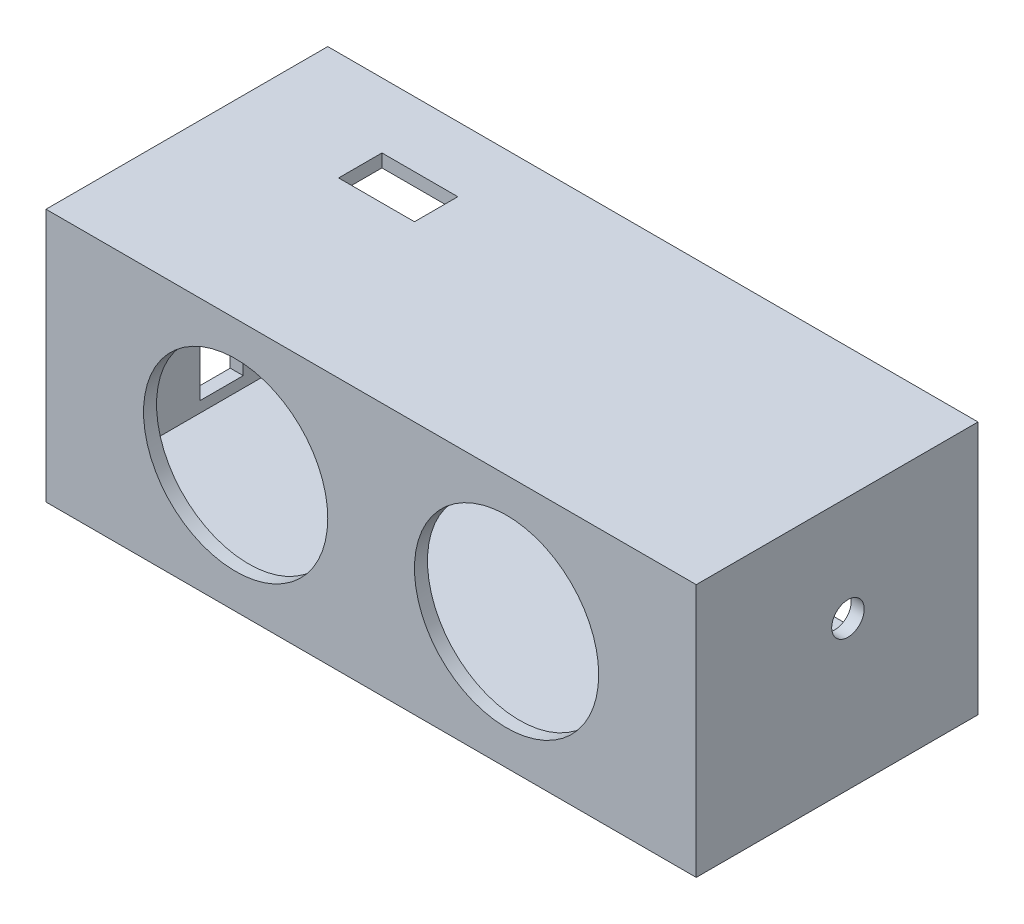
SolidWorks part; units mm, degrees
ref_plane "Front Plane" through (0, 0, 0) normal (0, 0, 1) x (1, 0, 0)
ref_plane "Top Plane" through (0, 0, 0) normal (0, 1, 0) x (1, 0, 0)
ref_plane "Right Plane" through (0, 0, 0) normal (1, 0, 0) x (0, 0, -1)
sketch3d "3DSketch1"
  line L0 (-25.7407, -9.0712, 0) -> (34.2593, -9.0712, 0)
  line L1 (-25.7407, 14.3288, 0) -> (34.2593, 14.3288, 0)
  line L2 (-25.7407, 14.3288, 0) -> (-25.7407, -9.0712, 0)
  line L4 (34.2593, 14.3288, 0) -> (34.2593, -9.0712, 0)
  circle A0 centre (-8.2407, 2.6288, 0) radius 8.5
  circle A1 centre (16.7593, 2.6288, 0) radius 8.5
  point P10 (-8.2407, 2.6288, 8.5)
  point P13 (16.7593, 2.6288, 8.5)
  dimension "D5" = 17
  dimension "D6" = 17
  dimension "D2" = 17.5
  dimension "D1" = 23.4
  dimension "D3" = 17.5
  dimension "D4" = 25
extrude "Boss-Extrude3" add sketch "3DSketch1" along direction (0, 0, 1) on the side of the normal blind 1.2
sketch "Sketch3" plane through (0, 0, 0) normal (0, 0, 1) x (1, 0, 0)
  line L1 (-25.7407, 14.3288) -> (34.2593, 14.3288)
  line L2 (-25.7407, 14.3288) -> (-25.7407, -9.0712)
  line L3 (-25.7407, -9.0712) -> (34.2593, -9.0712)
  line L4 (34.2593, 14.3288) -> (34.2593, -9.0712)
  line L5 (-24.5407, 13.1288) -> (33.0593, 13.1288)
  line L6 (-24.5407, 13.1288) -> (-24.5407, -7.8712)
  line L7 (-24.5407, -7.8712) -> (33.0593, -7.8712)
  line L8 (33.0593, 13.1288) -> (33.0593, -7.8712)
  dimension "D1" = 1.2
  dimension "D2" = 1.2
  dimension "D3" = 1.2
  dimension "D4" = 1.2
extrude "Boss-Extrude4" add sketch "Sketch3" against normal blind 26
sketch "Sketch6" plane through (0, -9.0712, 0) normal (0, -1, 0) x (1, 0, 0)
  line L0 (-25.7407, -26) -> (34.2593, -26) construction
  line L1 (34.2593, 0) -> (33.0593, 0)
  line L2 (34.2593, 0) -> (34.2593, -1.2)
  line L3 (34.2593, -1.2) -> (33.0593, -1.2)
  line L4 (33.0593, 0) -> (33.0593, -1.2)
  line L5 (33.0593, -1.2) -> (20.5593, -1.2)
  line L6 (33.0593, -1.2) -> (33.0593, -19.2)
  line L7 (33.0593, -19.2) -> (20.5593, -19.2)
  line L8 (20.5593, -1.2) -> (20.5593, -19.2)
  line L9 (20.5593, -9.2) -> (23.5593, -9.2)
  line L10 (20.5593, -9.2) -> (20.5593, -17.2)
  line L11 (20.5593, -17.2) -> (23.5593, -17.2)
  line L12 (23.5593, -9.2) -> (23.5593, -17.2)
  dimension "D1" = 1.2
  dimension "D2" = 1.2
  dimension "D3" = 18
  dimension "D4" = 12.5
  dimension "D5" = 8
  dimension "D6" = 2
  dimension "D7" = 3
extrude "Cut-Extrude1" cut sketch "Sketch6" against normal blind 4 contours L12 L9 L8 L11
sketch "Sketch7" plane through (0, 14.3288, 0) normal (0, 1, 0) x (1, 0, 0)
  line L0 (-25.7407, 0) -> (-25.7407, 26) construction
  line L1 (-25.7407, 26) -> (-7.7407, 26)
  line L2 (-25.7407, 26) -> (-25.7407, 20)
  line L3 (-25.7407, 20) -> (-7.7407, 20)
  line L4 (-7.7407, 26) -> (-7.7407, 20)
  line L5 (-7.7407, 20) -> (-14.7407, 20)
  line L6 (-7.7407, 20) -> (-7.7407, 16)
  line L7 (-7.7407, 16) -> (-14.7407, 16)
  line L8 (-14.7407, 20) -> (-14.7407, 16)
  dimension "D1" = 6
  dimension "D2" = 4
  dimension "D3" = 7
  dimension "D4" = 11
extrude "Cut-Extrude2" cut sketch "Sketch7" against normal blind 4 contours L3 L8 L7 L6
sketch "Sketch9" plane through (34.2593, 0, 0) normal (1, 0, 0) x (0, 0, -1)
  line L0 (0, 4.6288) -> (26, 4.6288)
  line L1 (26, -9.0712) -> (0, -9.0712)
  line L2 (26, -9.0712) -> (26, 14.3288)
  line L3 (26, 14.3288) -> (0, 14.3288)
  line L4 (0, -9.0712) -> (0, 14.3288)
  line L5 (26, 4.6288) -> (20, 4.6288)
  line L6 (20, 4.6288) -> (14, 4.6288)
  circle A0 centre (14, 4.6288) radius 6
  circle A1 centre (14, 4.6288) radius 1.5
  dimension "D4" = 3
  dimension "D1" = 13.7
  dimension "D2" = 6
  dimension "D3" = 6
extrude "Cut-Extrude4" cut sketch "Sketch9" against normal blind 4 contours L0 A1 | L0 A1
sketch "Sketch10" plane through (-25.7407, 0, 0) normal (-1, 0, 0) x (0, 0, 1)
  line L0 (0, 2.6288) -> (-8, 2.6288)
  line L1 (0, 14.3288) -> (0, -9.0712) construction
  line L2 (-8, 2.6288) -> (-17, 2.6288)
  line L5 (-26, 14.3288) -> (-26, -9.0712) construction
  line L6 (-26, 5.3979) -> (-20, 5.3979)
  line L7 (-17.2, -9.0712) -> (-17.2, -6.8712)
  line L9 (-17, -6.8712) -> (-13, -6.8712)
  line L10 (-17, -6.8712) -> (-17, 7.1288)
  line L11 (-17, 7.1288) -> (-13, 7.1288)
  line L12 (-13, -6.8712) -> (-13, 7.1288)
  dimension "D1" = 8
  dimension "D2" = 6
  dimension "D3" = 2.2
  dimension "D4" = 9
  dimension "D5" = 14
  dimension "D6" = 4
extrude "Cut-Extrude5" cut sketch "Sketch10" against normal blind 4 contours L2 L12 L11 L10 | L9 L12 L2 L10
